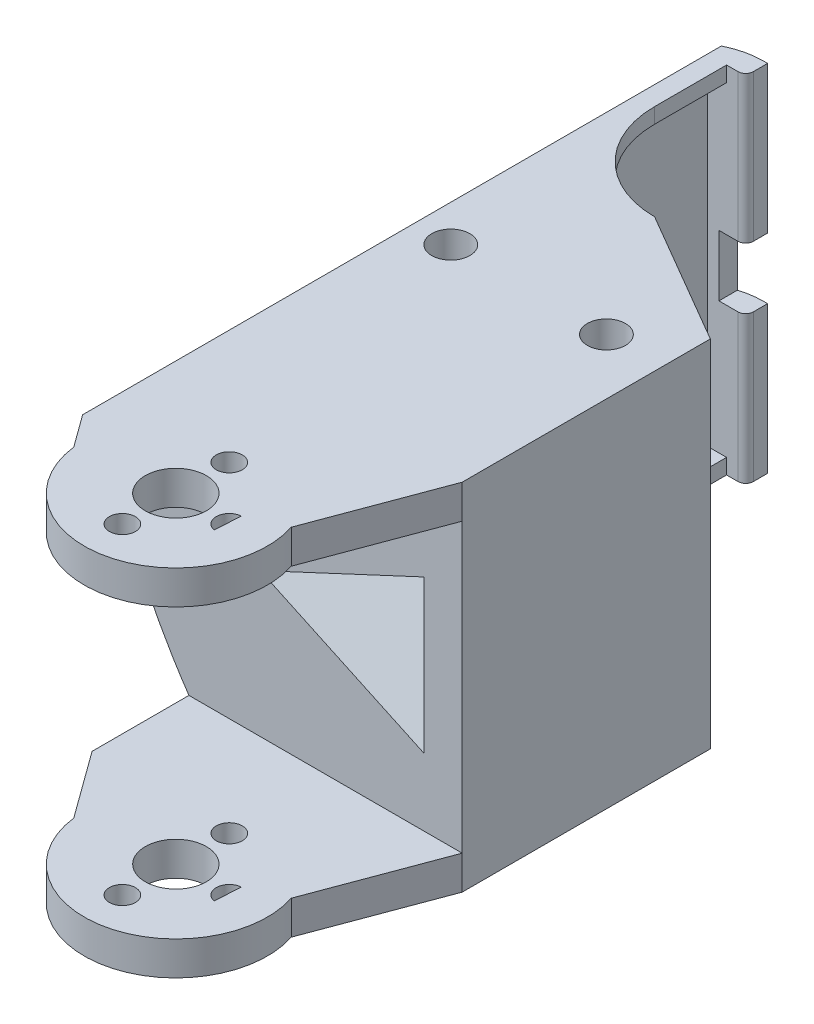
SolidWorks part; units mm, degrees
ref_plane "Front Plane" through (0, 0, 0) normal (0, 0, 1) x (1, 0, 0)
ref_plane "Top Plane" through (0, 0, 0) normal (0, 1, 0) x (1, 0, 0)
ref_plane "Right Plane" through (0, 0, 0) normal (1, 0, 0) x (0, 0, -1)
sketch "Sketch2" plane through (0, 0, 0) normal (0, 1, 0) x (1, 0, 0)
  line L0 (17.5, 0) -> (17.5, 37.7)
  line L1 (-15, 2.5) -> (15, 2.5)
  line L2 (-15, 2.5) -> (-15, 37.7)
  line L4 (15, 2.5) -> (15, 37.7)
  line L5 (17.5, 37.7) -> (15, 37.7)
  line L7 (-17.5, 37.7) -> (-17.5, 0)
  line L8 (-17.5, 0) -> (17.5, 0)
  line L10 (-17.5, 37.7) -> (-15, 37.7)
  point P4 (0, 2.5)
  point P12 (0, 0)
  dimension "D1" = 2.5
  dimension "D2" = 2.5
  dimension "D3" = 37.7
  dimension "D4" = 30
  dimension "D5" = 15
extrude "Boss-Extrude1" add sketch "Sketch2" along normal blind 32.5
sketch "Sketch4" plane through (0, 0, 0) normal (0, -1, 0) x (1, 0, 0)
  line L0 (-17.5, 0) -> (-17.5, -7.4438)
  line L8 (17.5, -7.4438) -> (17.5, 0)
  line L9 (17.5, 0) -> (-17.5, 0)
  line L10 (17.5, 0) -> (17.5, -37.7) construction
  line L13 (-17.5, -7.4438) -> (-17.5, -37.7)
  line L23 (-17.5, -37.7) -> (-15, -37.7)
  line L34 (-15, -37.7) -> (-15, -7.5)
  line L35 (-15, -2.5) -> (-15, -37.7) construction
  line L36 (-15, -7.5) -> (15, -7.5)
  line L37 (15, -37.7) -> (15, -2.5) construction
  line L38 (15, -7.5) -> (15, -37.7)
  line L39 (15, -37.7) -> (17.5, -37.7)
  line L40 (17.5, -37.7) -> (17.5, -7.4438)
  circle A2 centre (-10.1889, -4.95) radius 1.05
  circle A5 centre (10.1889, -4.95) radius 1.05
  dimension "D5" = 2.1
  dimension "D1" = 7.5
  dimension "D6" = 7.3111
  dimension "D7" = 4.95
  dimension "D8" = 7.3111
extrude "Boss-Extrude2" add sketch "Sketch4" along normal blind 2
sketch "Sketch7" plane through (0, -2, 0) normal (0, -1, 0) x (1, 0, 0)
  line L0 (-17.5, 0) -> (-17.5, -37.7)
  line L1 (-17.5, -37.7) -> (-15, -37.7)
  line L2 (-17.5, 0) -> (17.5, 0)
  line L4 (17.5, 0) -> (17.5, -37.7)
  line L5 (17.5, -37.7) -> (15, -37.7)
  line L6 (15, -37.7) -> (15, -7.5)
  line L7 (15, -7.5) -> (-15, -7.5)
  line L8 (-15, -7.5) -> (-15, -37.7)
  circle A2 centre (-10.1889, -4.95) radius 2.495
  circle A3 centre (10.1889, -4.95) radius 2.495
  dimension "D1" = 4.99
extrude "Wire spacing2" add sketch "Sketch7" along normal blind 3
sketch "Sketch8" plane through (0, -5, 0) normal (0, -1, 0) x (1, 0, 0)
  line L0 (-17.5, 0) -> (-17.5, -37.7)
  line L1 (-17.5, -37.7) -> (17.5, -37.7)
  line L2 (17.5, -37.7) -> (17.5, 0) construction
  line L3 (15, -37.7) -> (17.5, -37.7) construction
  line L4 (-17.5, 0) -> (17.5, 0)
  line L6 (17.5, 0) -> (17.5, -37.7)
  circle A0 centre (-10.1889, -4.95) radius 2.495
  circle A1 centre (10.1889, -4.95) radius 2.495
  circle A2 centre (10.1889, -4.95) radius 2.495 construction
  circle A3 centre (-10.1889, -4.95) radius 2.495 construction
extrude "Boss-Extrude6" add sketch "Sketch8" along normal blind 2
sketch "Sketch5" plane through (0, 32.5, 0) normal (0, 1, 0) x (1, 0, 0)
  line L0 (-7.439, 10) -> (-7.439, 2.5)
  line L9 (15, 2.5) -> (-15, 2.5) construction
  line L11 (-10.1889, 12) -> (-7.439, 10)
  line L13 (-17.5, 0) -> (17.5, 0) construction
  line L15 (-17.5, 0) -> (-17.5, 37.7)
  line L17 (10.1889, 12) -> (7.439, 10)
  line L20 (17.5, 0) -> (17.5, 37.7)
  line L21 (-7.439, 2.5) -> (7.439, 2.5)
  line L22 (7.439, 2.5) -> (7.439, 10)
  line L23 (-17.5, 0) -> (17.5, 0)
  line L24 (-10.1889, 12) -> (-15, 12)
  line L25 (-15, 37.7) -> (-15, 7.5) construction
  line L26 (-15, 12) -> (-15, 37.7)
  line L27 (-15, 37.7) -> (-17.5, 37.7)
  line L30 (17.5, 37.7) -> (15, 37.7)
  line L31 (15, 37.7) -> (15, 12)
  line L32 (15, 7.5) -> (15, 37.7) construction
  line L33 (15, 12) -> (10.1889, 12)
  circle A0 centre (-10.1889, 4.95) radius 1.05 construction
  circle A1 centre (-10.1889, 8.7) radius 1.05
  circle A2 centre (10.1889, 8.7) radius 1.05
  circle A3 centre (10.1889, 4.95) radius 1.05 construction
  dimension "D4" = 0
  dimension "D7" = 8.7
  dimension "D3" = 0
  dimension "D1" = 12
  dimension "D2" = 10.061
  dimension "D5" = 10
  dimension "D6" = 10.061
extrude "Boss-Extrude3" add sketch "Sketch5" along normal blind 2
sketch "Sketch9" plane through (0, 34.5, 0) normal (0, 1, 0) x (1, 0, 0)
  line L0 (-17.5, 0) -> (-17.5, 37.7)
  line L1 (-17.5, 37.7) -> (-15, 37.7)
  line L2 (-15, 37.7) -> (-15, 12)
  line L3 (-15, 12) -> (-10.1889, 12)
  line L4 (-10.1889, 12) -> (-7.439, 10)
  line L5 (-7.439, 10) -> (-7.439, 2.5)
  line L6 (-7.439, 2.5) -> (7.439, 2.5)
  line L7 (7.439, 2.5) -> (7.439, 10)
  line L8 (7.439, 10) -> (10.1889, 12)
  line L9 (10.1889, 12) -> (7.439, 10) construction
  line L10 (10.1889, 12) -> (15, 12)
  line L11 (15, 7.5) -> (15, 37.7) construction
  line L12 (15, 12) -> (15, 37.7)
  line L13 (15, 37.7) -> (17.5, 37.7)
  line L14 (17.5, 0) -> (17.5, 37.7) construction
  line L15 (17.5, 37.7) -> (15, 37.7) construction
  line L16 (17.5, 37.7) -> (17.5, 0)
  line L17 (17.5, 0) -> (-17.5, 0)
  line L18 (15, 12) -> (10.1889, 12) construction
  circle A0 centre (-10.1889, 8.7) radius 2.495
  circle A1 centre (10.1889, 8.7) radius 2.495
  dimension "D1" = 4.99
  dimension "D2" = 0
extrude "Wire spacing1" add sketch "Sketch9" along normal blind 3
sketch "Sketch10" plane through (0, 37.5, 0) normal (0, 1, 0) x (1, 0, 0)
  line L1 (-17.5, 37.7) -> (17.5, 37.7)
  line L2 (-17.5, 37.7) -> (-17.5, 0)
  line L3 (-17.5, 0) -> (17.5, 0)
  line L4 (17.5, 37.7) -> (17.5, 0)
  circle A0 centre (-10.1889, 8.7) radius 2.495
  circle A1 centre (10.1889, 8.7) radius 2.495
  circle A2 centre (-10.1889, 8.7) radius 2.495 construction
  circle A3 centre (10.1889, 8.7) radius 2.495 construction
extrude "Boss-Extrude8" add sketch "Sketch10" along normal blind 2
sketch "Sketch11" plane through (0, 39.5, 0) normal (0, 1, 0) x (1, 0, 0)
  line L0 (17.5, 37.7) -> (-17.5, 37.7) construction
  circle A0 centre (0, 37.7) radius 12.5
  dimension "D1" = 25
extrude "Cut-Extrude1" cut sketch "Sketch11" against normal through all
sketch "Sketch12" plane through (0, -7, 0) normal (0, -1, 0) x (1, 0, 0)
  line L4 (0, -25.2) -> (17.5, -15)
  line L5 (17.5, -37.7) -> (17.5, 0) construction
  line L6 (17.5, -15) -> (17.5, -47.4845)
  line L7 (17.5, -47.4845) -> (0, -25.2)
  line L8 (17.5, 0) -> (-17.5, 0) construction
  arc A1 (12.5, -37.7) -> (-12.5, -37.7) centre (0, -37.7) ccw construction
  dimension "D1" = 15
extrude "Cut-Extrude2" cut sketch "Sketch12" against normal through all
sketch "Sketch13" plane through (0, 0, 0) normal (0, 0, 1) x (1, 0, 0)
  line L0 (17.5, -7) -> (-17.5, -7) construction
  line L1 (17.5, 39.5) -> (-27.5, 39.5)
  line L2 (17.5, 39.5) -> (17.5, -7)
  line L3 (17.5, -7) -> (-27.5, -7)
  line L4 (-27.5, 39.5) -> (-27.5, -7)
  line L5 (-17.5, 39.5) -> (-17.5, -7) construction
  dimension "D1" = 10
extrude "Boss-Extrude9" add sketch "Sketch13" along normal blind 17.5
sketch "Sketch15" plane through (0, 0, 0) normal (0, 0, -1) x (-1, 0, 0)
  line L0 (17.5, -7) -> (12.5, -7) construction
  line L1 (27.5, 39.5) -> (15, 39.5)
  line L2 (27.5, 39.5) -> (27.5, -7)
  line L3 (27.5, -7) -> (15, -7)
  line L4 (15, 39.5) -> (15, -7)
extrude "Boss-Extrude10" add sketch "Sketch15" along normal blind 50
sketch "Sketch18" plane through (0, -7, 0) normal (0, -1, 0) x (1, 0, 0)
  line L0 (12.5, 22.5) -> (12.5, 17.5)
  line L1 (12.5, 17.5) -> (-12.5, 17.5)
  line L2 (-12.5, 22.5) -> (-12.5, 17.5)
  line L3 (12.5, 22.5) -> (9.3675, 30)
  line L4 (-9.3675, 30) -> (-12.5, 22.5)
  line L5 (-27.5, 17.5) -> (17.5, 17.5) construction
  circle A0 centre (0, 37.5) radius 4
  arc A1 (9.3675, 30) -> (-9.3675, 30) centre (0, 37.5) ccw
  circle A2 centre (0, 30.5) radius 1.7
  circle A3 centre (-7, 37.5) radius 1.7
  circle A4 centre (0, 44.5) radius 1.7
  circle A5 centre (7, 37.5) radius 1.7
  point P11 (7.7726, 26.3901)
  point P12 (0, 17.5)
  dimension "D3" = 8
  dimension "D5" = 12
  dimension "D7" = 3.4
  dimension "D1" = 25
  dimension "D2" = 20
  dimension "D4" = 5
  dimension "D6" = 12.5
  dimension "D8" = 7
  dimension "D9" = 7
  dimension "D10" = 7
  dimension "D11" = 7
  dimension "D12" = 0
  dimension "D13" = 0
extrude "Boss-Extrude11" add sketch "Sketch18" against normal up to surface (46.5 mm away) up to face at (-8.1361, 39.5, -22.2514)
sketch "Sketch22" plane through (0, -7, 0) normal (0, -1, 0) x (1, 0, 0)
  line L0 (-27.5, 17.5) -> (-5.0663, 48.3781)
  line L1 (-5.0663, 48.3781) -> (-5.0663, 17.5)
  line L2 (-5.0663, 17.5) -> (-27.5, 17.5)
  line L4 (17.5, 17.5) -> (6.1943, 47.7777)
  line L5 (6.1943, 47.7777) -> (7.9223, 17.5)
  line L6 (7.9223, 17.5) -> (17.5, 17.5)
  arc A0 (9.3675, 30) -> (-9.3675, 30) centre (0, 37.5) ccw construction
extrude "Boss-Extrude13" add sketch "Sketch22" against normal up to surface (46.5 mm away) up to face at (-4.6492, 39.5, -1.3222)
sketch "Sketch21" plane through (-27.5, 0, 0) normal (-1, 0, 0) x (0, 0, 1)
  line L1 (107.4125, 35.075) -> (17.5, 35.075)
  line L2 (107.4125, 35.075) -> (107.4125, -2.575)
  line L3 (107.4125, -2.575) -> (17.5, -2.575)
  line L4 (17.5, 35.075) -> (17.5, -2.575)
  line L6 (-50, -7) -> (-50, 39.5) construction
  line L7 (17.5, 39.5) -> (17.5, -7) construction
  point P6 (-50, 16.25)
  point P7 (17.5, 16.25)
  dimension "D1" = 37.65
  dimension "D2" = 0
extrude "Cut-Extrude3" cut sketch "Sketch21" against normal through all
sketch "Sketch26" plane through (0, 39.5, 0) normal (0, 1, 0) x (1, 0, 0)
  line L0 (-27.5, -17.5) -> (-27.5, 50) construction
  line L1 (-27.5, 29.3872) -> (-27.5, 50)
  line L2 (-27.5, 50) -> (-15, 50)
  spline S0 degree 2 poles (-15, 50) (-23.5947, 41.1535) (-27.5, 29.3872) knots 0 0 0 1 1 1
extrude "Cut-Extrude5" cut sketch "Sketch26" against normal through all
sketch "Sketch24" plane through (0, 0, 0) normal (0, 0, -1) x (-1, 0, 0)
  line L4 (15, -7) -> (27.5, -7)
  line L5 (27.5, -7) -> (27.5, 16.25)
  spline S0 degree 2 poles (27.5, 16.25) (23.3985, 3.4824) (15, -7) knots 0 0 0 1 1 1
extrude "Cut-Extrude4" cut sketch "Sketch24" against normal through all both and the other way through all
ref_plane "Plane1" through (0, 16.25, 0) normal (0, -1, 0) x (-1, 0, 0)
mirror "Mirror1" about plane through (0, 16.25, 0) normal (0, -1, 0) of "Cut-Extrude4"
sketch "Sketch27" plane through (0, 0, -2.5) normal (0, 0, -1) x (-1, 0, 0)
  line L0 (-12.5, 26.25) -> (8.9451, 16.25)
  line L1 (-17.875, 16.25) -> (17.875, 16.25) construction
  line L2 (8.9451, 16.25) -> (-12.5, 6.25)
  line L4 (-12.5, 6.25) -> (-12.5, 26.25)
  line L5 (-15, 32.5) -> (-15, 0) construction
  point P7 (-12.5, 16.25)
  dimension "D1" = 50
  dimension "D2" = 20
  dimension "D3" = 2.5
extrude "Cut-Extrude6" cut sketch "Sketch27" against normal through all
sketch "Sketch28" plane through (0, 39.5, 0) normal (0, 1, 0) x (1, 0, 0)
  line L0 (-15, 37.7) -> (-15, 50)
  line L1 (-15, 50) -> (-10, 50)
  line L2 (-10, 50) -> (-10, 47.127)
  line L3 (-10, 47.127) -> (-12.5, 47.127)
  line L4 (-12.5, 47.127) -> (-12.5, 37.7)
  line L5 (-15, 37.7) -> (-12.5, 37.7)
  dimension "D1" = 2.5
extrude "Boss-Extrude14" add sketch "Sketch28" against normal up to surface (46.5 mm away) up to face at (-0.9682, -7, 3.0985)
fillet "Fillet2" radius 10 1 edges at (-15, 16.25, -50)
sketch "Sketch29" plane through (0, 0, -37.7) normal (0, 0, 1) x (1, 0, 0)
  line L1 (-15, 37.5) -> (-12.5, 37.5)
  line L2 (-15, 37.5) -> (-15, -5)
  line L3 (-15, -5) -> (-12.5, -5)
  line L4 (-12.5, 37.5) -> (-12.5, -5)
extrude "Cut-Extrude8" cut sketch "Sketch29" against normal up to surface (9.427 mm away) up to face at (-11.25, 16.25, -47.127)
fillet "Fillet3" radius 1 1 edges at (-10, 16.25, -47.127)
sketch "Sketch30" plane through (0, 0, -47.127) normal (0, 0, 1) x (1, 0, 0)
  line L0 (-17.875, 16.25) -> (17.875, 16.25) construction
  line L1 (-6.1884, 20.25) -> (-13.5, 20.25)
  line L2 (-6.1884, 20.25) -> (-6.1884, 12.25)
  line L3 (-6.1884, 12.25) -> (-13.5, 12.25)
  line L4 (-13.5, 20.25) -> (-13.5, 12.25)
  line L5 (-11, -7) -> (-11, 39.5) construction
  point P4 (-13.5, 16.25)
  dimension "D1" = 8
  dimension "D2" = 2.5
extrude "Cut-Extrude9" cut sketch "Sketch30" against normal blind 22.5
